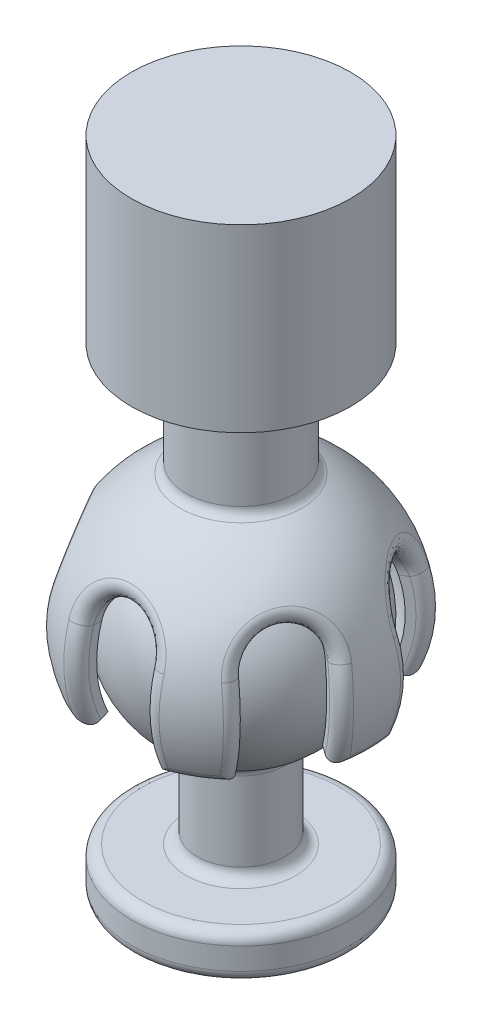
SolidWorks part; units mm, degrees
other "Socket"
other "Ball"
material "PE High Density"
ref_plane "Front Plane" through (0, 0, 0) normal (0, 0, 1) x (1, 0, 0)
ref_plane "Top Plane" through (0, 0, 0) normal (0, 1, 0) x (1, 0, 0)
ref_plane "Right Plane" through (0, 0, 0) normal (1, 0, 0) x (0, 0, -1)
sketch "Sketch2" plane through (0, 0, 0) normal (0, 0, 1) x (1, 0, 0)
  line L0 (0, 14.7525) -> (0, -5.2213) construction
  line L1 (0, -2) -> (4.5, -2)
  line L2 (5, -1.5) -> (5, -0.5)
  line L3 (4.5, 0) -> (2.5, 0)
  line L4 (2, 0.5) -> (2, 4.101)
  line L5 (0, 11) -> (0, -2)
  line L7 (0, 11) -> (0, 14)
  arc A0 (0, 14) -> (2.2727, 4.5464) centre (0, 9) cw
  arc A1 (2, 4.101) -> (2.2727, 4.5464) centre (2.5, 4.101) cw
  arc A2 (2.5, 0) -> (2, 0.5) centre (2.5, 0.5) cw
  arc A3 (5, -0.5) -> (4.5, 0) centre (4.5, -0.5) ccw
  arc A4 (4.5, -2) -> (5, -1.5) centre (4.5, -1.5) ccw
  point P12 (0, 0)
  point P16 (2, 4)
  point P19 (2, 0)
  point P22 (5, 0)
  point P25 (5, -2)
  dimension "D7" = 0.5
  dimension "D6" = 5
  dimension "D1" = 2
  dimension "D2" = 4
  dimension "D3" = 3
  dimension "D4" = 2
  dimension "D5" = 5
  dimension "D8" = 16
revolve "Joystick" add sketch "Sketch2" angle 360 about L0
sketch "Sketch3" plane through (0, 0, 0) normal (0, 0, 1) x (1, 0, 0)
  line L0 (-4.8034, 6.7601) -> (-5.7097, 6.3375)
  line L1 (0, 9) -> (0, 28) construction
  line L2 (0, 14.3) -> (0, 28)
  line L3 (0, 28) -> (-5, 28)
  line L4 (-5, 28) -> (-5, 19.7827)
  line L5 (-5, 19.7827) -> (-2.5, 19.7827)
  line L6 (-2.5, 19.7827) -> (-2.5, 14.7827)
  arc A0 (2.8636, 3.3884) -> (-2.8636, 3.3884) centre (0, 9) ccw construction
  arc A1 (-2.5, 14.7827) -> (-5.7097, 6.3375) centre (0, 9) ccw
  arc A2 (2.4091, 4.2792) -> (-2.4091, 4.2792) centre (0, 9) ccw
  arc A3 (0, 14.3) -> (-4.8034, 6.7601) centre (0, 9) ccw
  arc A4 (2.4091, 4.2792) -> (-2.4091, 4.2792) centre (0, 9) ccw construction
  point P15 (0, 0)
  point P16 (0, 0)
  dimension "D3" = 25
  dimension "D4" = 13.7
  dimension "D5" = 5
  dimension "D6" = 2.5
  dimension "D7" = 5
  dimension "D1" = 0.3
  dimension "D2" = 1
revolve "Revolve2" add sketch "Sketch3" angle 360 about L1
sketch "Sketch4" plane through (0, 0, 0) normal (0, 0, 1) x (1, 0, 0)
  line L0 (0, 10.5) -> (0, 4.5) construction
  line L1 (1.5, 10.5) -> (1.5, 4.5)
  line L2 (-1.5, 10.5) -> (-1.5, 4.5)
  arc A0 (1.5, 10.5) -> (-1.5, 10.5) centre (0, 10.5) ccw
  arc A1 (-1.5, 4.5) -> (1.5, 4.5) centre (0, 4.5) ccw
  point P3 (0, 7.5)
  dimension "D1" = 1.5
  dimension "D3" = 4.5
  dimension "D2" = 3
extrude "Cut-Extrude1" cut sketch "Sketch4" against normal through all both and the other way through all
pattern_circular "CirPattern1" count 6 over 360 about axis through (0, 0, 0) along (0, 1, 0) of "Cut-Extrude1"
fillet "Fillet1" radius 0.5 25 edges at (2.5, 14.7827, 0) (-1.5, 8.3815, 6.0875) (-1.5, 8.3815, -6.0875) (0.2128, 11.9848, 5.544) (-0.2128, 11.9848, -5.544) (1.5, 8.3815, 6.0875) (1.5, 8.3815, -6.0875) (2.8549, 6.3375, -4.9448) (4.5219, 8.3815, -4.3428) (4.6948, 11.9848, -2.9563) (6.0219, 8.3815, -1.7447) (5.7097, 6.3375, 0) (6.0219, 8.3815, 1.7447) (4.9076, 11.9848, 2.5877) (4.5219, 8.3815, 4.3428) (2.8549, 6.3375, 4.9448) (-2.8549, 6.3375, 4.9448) (-4.5219, 8.3815, 4.3428) (-4.6948, 11.9848, 2.9563) (-6.0219, 8.3815, 1.7447) (-5.7097, 6.3375, 0) (-6.0219, 8.3815, -1.7447) (-4.9076, 11.9848, -2.5877) (-4.5219, 8.3815, -4.3428) (-2.8549, 6.3375, -4.9448)
